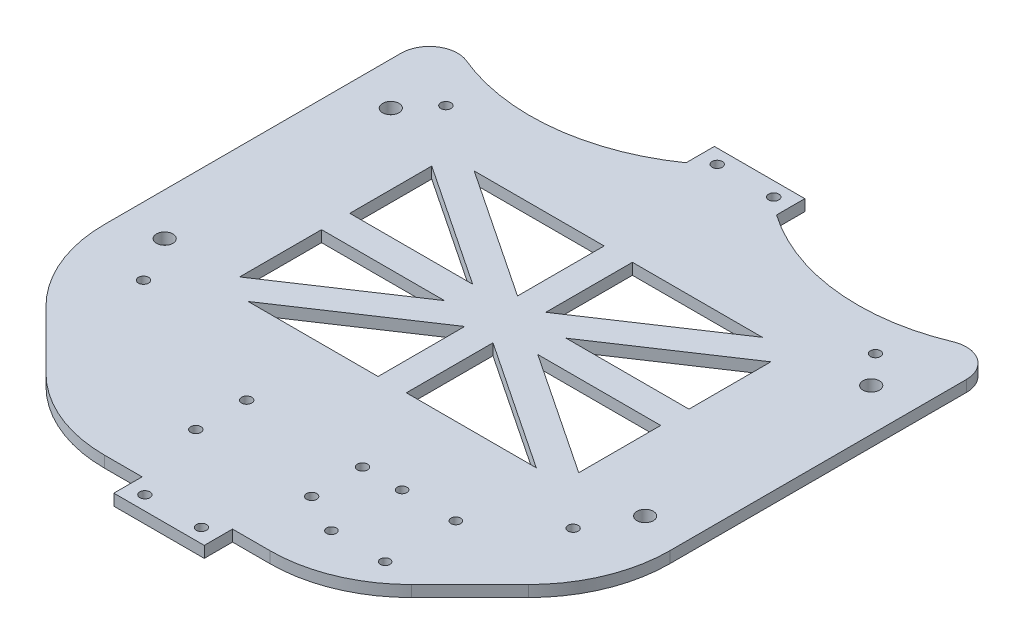
SolidWorks part; units mm, degrees
material "PLA"
ref_plane "Front Plane" through (0, 0, 0) normal (0, 0, 1) x (1, 0, 0)
ref_plane "Top Plane" through (0, 0, 0) normal (0, 1, 0) x (1, 0, 0)
ref_plane "Right Plane" through (0, 0, 0) normal (1, 0, 0) x (0, 0, -1)
sketch "Sketch1" plane through (0, 0, 0) normal (0, 1, 0) x (1, 0, 0)
  line L0 (-100, -222) -> (100, -222)
  line L1 (100, -222) -> (100, -29.5)
  line L2 (100, -29.5) -> (16, -29.5) construction
  line L3 (16, -29.5) -> (16, -19.5)
  line L10 (-16, -29.5) -> (-100, -29.5) construction
  line L11 (-100, -29.5) -> (-100, -222)
  line L12 (0, -222) -> (0, 5.5) construction
  line L17 (-10, -24.5) -> (10, -24.5) construction
  line L18 (-16, -29.5) -> (16, -29.5) construction
  line L19 (-10, -227) -> (10, -227) construction
  line L20 (-16.5139, -104.5) -> (-60, -104.5)
  line L21 (-60, -114.5) -> (-16.5139, -114.5)
  line L22 (-5, -118.8426) -> (-5, -149.5)
  line L27 (5, -118.8426) -> (5, -149.5)
  line L28 (60, -109.5) -> (-60, -109.5) construction
  line L29 (60, -114.5) -> (16.5139, -114.5)
  line L30 (16.5139, -104.5) -> (60, -104.5)
  line L31 (5, -100.1574) -> (5, -69.5)
  line L32 (-5, -100.1574) -> (-5, -69.5)
  line L54 (-60, -69.5) -> (-60, -149.5)
  line L55 (-60, -149.5) -> (60, -149.5)
  line L56 (60, -149.5) -> (60, -69.5)
  line L57 (60, -69.5) -> (-60, -69.5)
  line L59 (-16, -19.5) -> (16, -19.5)
  line L61 (-16, -222) -> (-16, -232)
  line L62 (-16, -232) -> (16, -232)
  line L63 (16, -232) -> (16, -222)
  line L64 (17, -183) -> (17, -210)
  line L65 (17, -210) -> (-18, -210)
  line L66 (-18, -210) -> (-18, -183)
  line L67 (-18, -183) -> (17, -183)
  line L68 (-21, -198) -> (-21, -180) construction
  line L69 (-21, -180) -> (20, -180) construction
  line L70 (20, -180) -> (20, -198) construction
  line L74 (-60, -75.5093) -> (50.9861, -149.5)
  line L75 (60, -143.4907) -> (-50.9861, -69.5)
  line L76 (-60, -143.4907) -> (50.9861, -69.5)
  line L77 (-50.9861, -149.5) -> (60, -75.5093)
  line L78 (60, -69.5) -> (-60, -149.5) construction
  line L79 (-60, -69.5) -> (60, -149.5) construction
  line L81 (-16, -19.5) -> (-16, -29.5)
  arc A11 (16, -29.5) -> (100, -29.5) centre (58, 30.5) ccw
  arc A12 (-16, -29.5) -> (-100, -29.5) centre (-58, 30.5) cw
  point P5 (-76, -161.5)
  point P6 (-76, -54.5)
  point P7 (76, -161.5)
  point P8 (76, -54.5)
  point P10 (-10, -24.5)
  point P11 (10, -24.5)
  point P12 (0, -222)
  point P27 (0, -109.5)
  point P37 (0, -109.5)
  point P53 (0, -232)
  point P58 (-21, -180)
  point P59 (-21, -198)
  point P60 (20, -180)
  point P62 (20, -198)
  point P69 (-0.5, -180)
  point P70 (-0.5, -183)
  point P131 (-85, -65)
  point P132 (-85, -145)
  point P133 (85, -145)
  point P134 (85, -65)
  dimension "D29" = 22
  dimension "D30" = 10
  dimension "D31" = 27
  dimension "D39" = 3
  dimension "D12" = 152
  dimension "D13" = 60
  dimension "D4" = 200
  dimension "D8" = 30.5
  dimension "D9" = 192.5
  dimension "D10" = 10
  dimension "D11" = 16
  dimension "D14" = 107
  dimension "D15" = 25
  dimension "D16" = 20
  dimension "D17" = 5
  dimension "D18" = 20
  dimension "D19" = 40
  dimension "D20" = 10
  dimension "D21" = 10
  dimension "D32" = 35
  dimension "D33" = 17
  dimension "D37" = 18
  dimension "D38" = 41
  dimension "D58" = 120
  dimension "D60" = 80
  dimension "D67" = 80
  dimension "D68" = 170
  dimension "D69" = 77
  dimension "D75" = 10
  dimension "D76" = 10
extrude "Boss-Extrude1" add sketch "Sketch1" along normal blind 4
hole_wizard "M5 Clearance Hole1" positions "Sketch15" profile "Sketch14" hole size "M5" standard "ISO" end condition through all
sketch "Sketch15" plane through (0, 4, 0) normal (0, 1, 0) x (1, 0, 0)
  point P0 (-85, -65)
  point P3 (-85, -145)
  point P6 (85, -145)
  point P9 (85, -65)
sketch "Sketch14" plane through (-85, 4, 65) normal (1, 0, 0) x (0, 0, 1)
  line L0 (0, 0) -> (0, 4)
  line L1 (0, 4) -> (2.9, 4)
  line L2 (2.9, 4) -> (2.9, 0)
  line L5 (2.9, 0) -> (0, 0)
  line L11 (0, -6.35) -> (0, 107.95) construction
  dimension "Thru Hole Dia." = 5.8
  dimension "Thru Hole Depth" = 4
fillet "Fillet1" radius 10 2 edges at (100, 2, 29.5) (-100, 2, 29.5)
hole_wizard "M3 Clearance Hole1" positions "Sketch16" profile "Sketch17" hole size "M3" standard "ISO"
sketch "Sketch16" plane through (0, 4, 0) normal (0, 1, 0) x (1, 0, 0)
  point P0 (-21, -198)
  point P3 (-21, -180)
  point P6 (20, -180)
  point P9 (20, -198)
sketch "Sketch17" plane through (-21, 4, 198) normal (1, 0, 0) x (0, 0, 1)
  line L0 (0, 0) -> (0, 11.0815)
  line L1 (0, 11.0815) -> (1.8, 10)
  line L2 (1.8, 10) -> (1.8, 0)
  line L5 (1.8, 0) -> (0, 0)
  line L10 (0, 11.0815) -> (-1.8, 10) construction
  line L11 (0, -6.35) -> (0, 107.95) construction
  dimension "Hole Dia." = 3.6
  dimension "Hole Depth" = 10
  dimension "Drill Angle" = 118
chamfer "Chamfer1" distance 50 angle 45 2 edges at (100, 2, 222) (-100, 2, 222)
fillet "Fillet3" radius 50 4 edges at (-100, 2, 172) (-50, 2, 222) (100, 2, 172) (50, 2, 222)
hole_wizard "M3 Clearance Hole2" positions "Sketch18" profile "Sketch19" hole size "M3" standard "ISO" end condition through all
sketch "Sketch18" plane through (0, 4, 0) normal (0, 1, 0) x (1, 0, 0)
  point P0 (-76, -54.5)
  point P3 (76, -54.5)
  point P6 (76, -161.5)
  point P9 (-76, -161.5)
  point P12 (-10, -24.5)
  point P15 (10, -24.5)
  point P19 (-10, -227)
  point P22 (10, -227)
sketch "Sketch19" plane through (-76, 4, 54.5) normal (1, 0, 0) x (0, 0, 1)
  line L0 (0, 0) -> (0, 4)
  line L1 (0, 4) -> (1.8, 4)
  line L2 (1.8, 4) -> (1.8, 0)
  line L5 (1.8, 0) -> (0, 0)
  line L11 (0, -6.35) -> (0, 107.95) construction
  dimension "Thru Hole Dia." = 3.6
  dimension "Thru Hole Depth" = 4
sketch "Sketch20" plane through (0, 4, 0) normal (0, 1, 0) x (1, 0, 0)
  line L0 (16, -222) -> (29.2893, -222) construction
  line L1 (53, -180) -> (34, -180) construction
  line L2 (53, -180) -> (53, -205) construction
  line L3 (53, -205) -> (34, -205) construction
  line L4 (34, -180) -> (34, -205) construction
  line L5 (53, -180) -> (34, -205) construction
  line L6 (53, -205) -> (34, -180) construction
  circle A0 centre (20, -198) radius 1.8 construction
  point P0 (43.5, -192.5)
  dimension "D1" = 25
  dimension "D2" = 19
  dimension "D3" = 17
  dimension "D4" = 14
hole_wizard "M3 Clearance Hole3" positions "Sketch23" profile "Sketch24" hole size "M3" standard "ISO" end condition through all
sketch "Sketch23" plane through (0, 4, 0) normal (0, 1, 0) x (1, 0, 0)
  point P0 (53, -180)
  point P3 (34, -180)
  point P6 (34, -205)
  point P9 (53, -205)
sketch "Sketch24" plane through (53, 4, 180) normal (1, 0, 0) x (0, 0, 1)
  line L0 (0, 0) -> (0, 4)
  line L1 (0, 4) -> (1.7, 4)
  line L2 (1.7, 4) -> (1.7, 0)
  line L5 (1.7, 0) -> (0, 0)
  line L11 (0, -6.35) -> (0, 107.95) construction
  dimension "Thru Hole Dia." = 3.4
  dimension "Thru Hole Depth" = 4
equation "\"w9\"=2"
